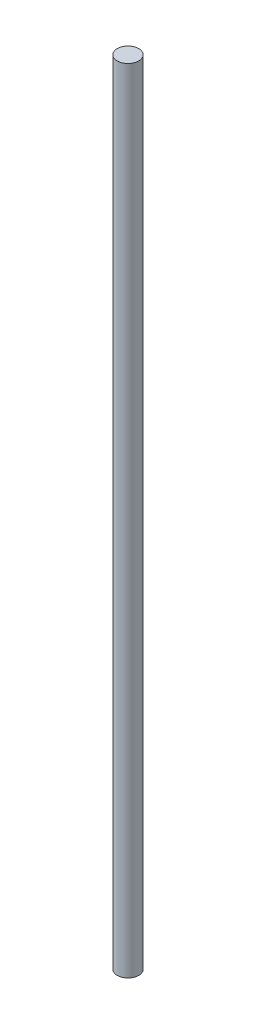
SolidWorks part; units mm, degrees
ref_plane "Front Plane" through (0, 0, 0) normal (0, 0, 1) x (1, 0, 0)
ref_plane "Top Plane" through (0, 0, 0) normal (0, 1, 0) x (1, 0, 0)
ref_plane "Right Plane" through (0, 0, 0) normal (1, 0, 0) x (0, 0, -1)
sketch "Sketch1" plane through (0, 0, 0) normal (0, 1, 0) x (1, 0, 0)
  circle A0 centre (0, 0) radius 4
  dimension "D1" = 8
extrude "Boss-Extrude1" add sketch "Sketch1" along normal blind 295
